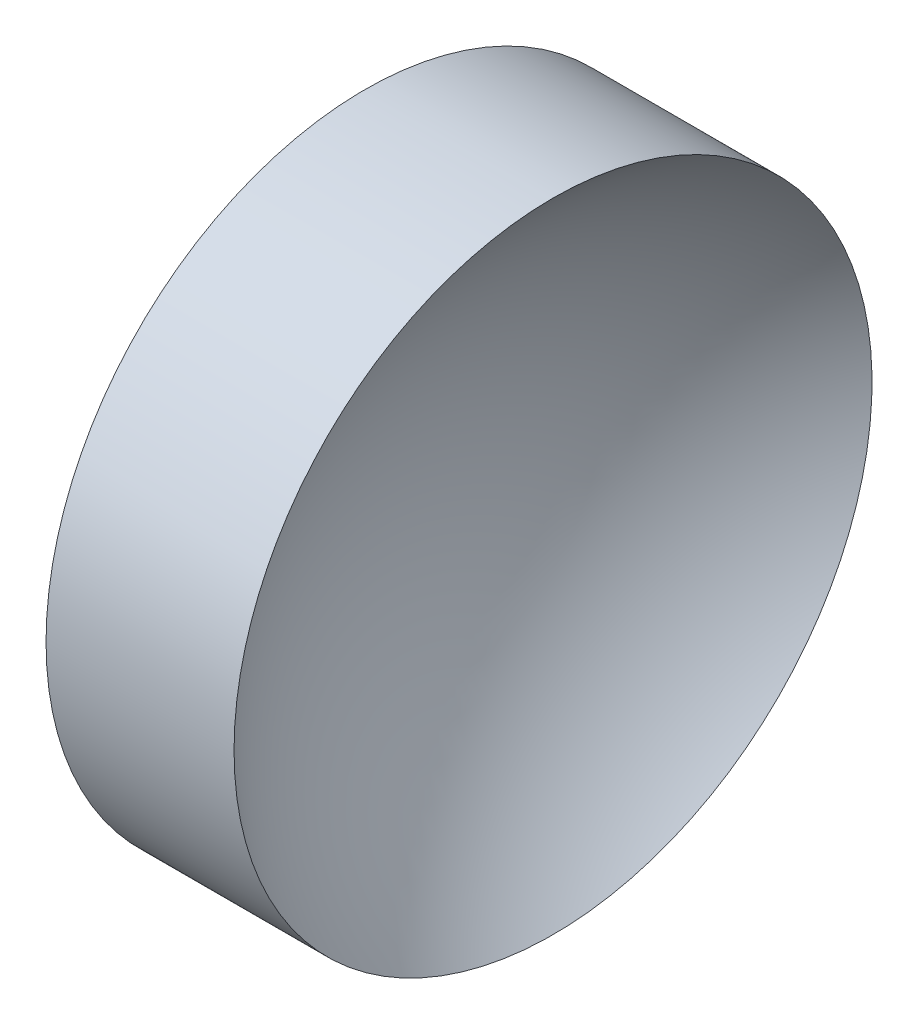
SolidWorks part; units mm, degrees
ref_plane "前视基准面" through (0, 0, 0) normal (0, 0, 1) x (1, 0, 0)
ref_plane "上视基准面" through (0, 0, 0) normal (0, 1, 0) x (1, 0, 0)
ref_plane "右视基准面" through (0, 0, 0) normal (1, 0, 0) x (0, 0, -1)
sketch "草图1" plane through (0, 0, 0) normal (0, 0, 1) x (1, 0, 0)
  line L0 (105.6218, 65.1556) -> (137.1869, 65.1556) construction
  line L1 (113.7394, 65.1556) -> (113.7394, 90.1556)
  line L2 (113.7394, 90.1556) -> (128.4729, 90.1556)
  line L3 (116.7394, 65.1556) -> (113.7394, 65.1556)
  arc A0 (128.4729, 90.1556) -> (116.7394, 65.1556) centre (149.2394, 65.1556) ccw
revolve "旋转1" add sketch "草图1" angle 360 about L0
